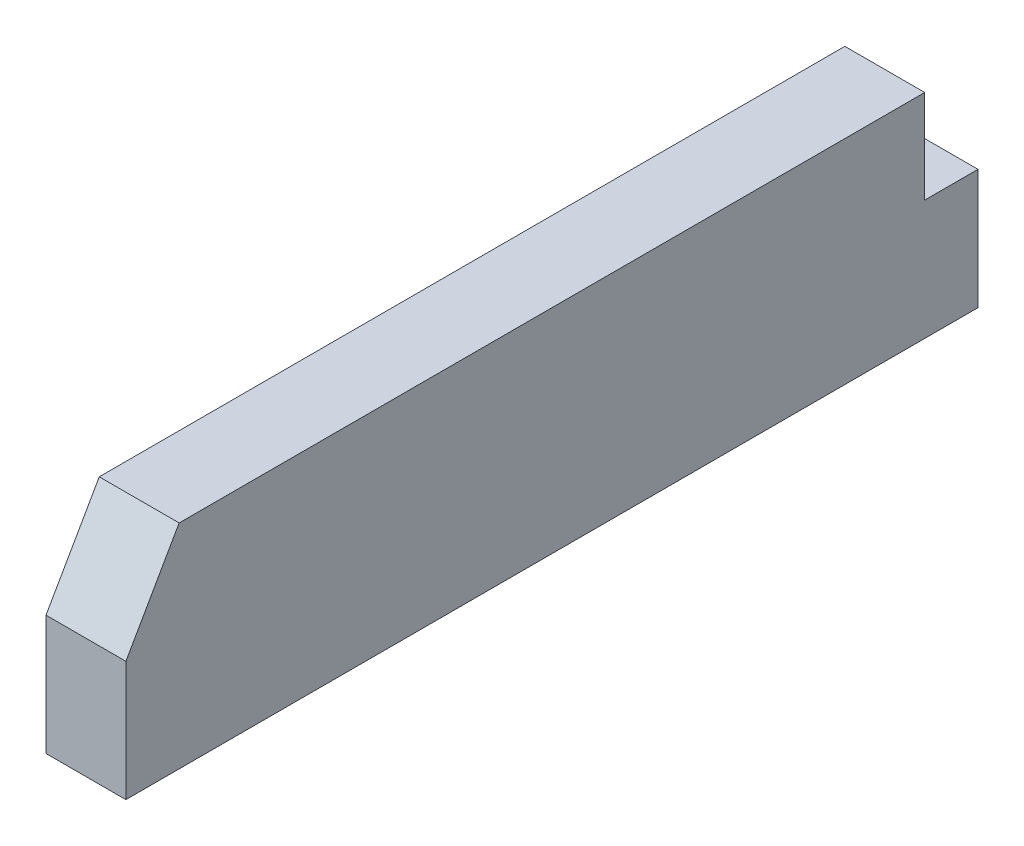
SolidWorks part; units mm, degrees
material "CA"
ref_plane "Front Plane" through (0, 0, 0) normal (0, 0, 1) x (1, 0, 0)
ref_plane "Top Plane" through (0, 0, 0) normal (0, 1, 0) x (1, 0, 0)
ref_plane "Right Plane" through (0, 0, 0) normal (1, 0, 0) x (0, 0, -1)
sketch "Sketch2" plane through (0, 0, 0) normal (1, 0, 0) x (0, 0, -1)
  line L0 (0, 0) -> (-88.9, 0)
  line L2 (-95.25, -25.4) -> (6.35, -25.4)
  line L3 (6.35, -25.4) -> (6.35, -11.1125)
  line L4 (6.35, -11.1125) -> (0, -11.1125)
  line L5 (0, -11.1125) -> (0, 0)
  line L6 (-88.9, 0) -> (-95.25, -11.1125)
  line L7 (-95.25, -11.1125) -> (-95.25, -25.4)
  point P3 (22.0223, -38.0521)
  point P9 (0, 0)
  dimension "D1" = 101.6
  dimension "D2" = 88.9
  dimension "D3" = 11.1125
  dimension "D4" = 25.4
  dimension "D5" = 11.1125
  dimension "D6" = 6.35
extrude "Boss-Extrude1" add sketch "Sketch2" along normal blind 9.525
